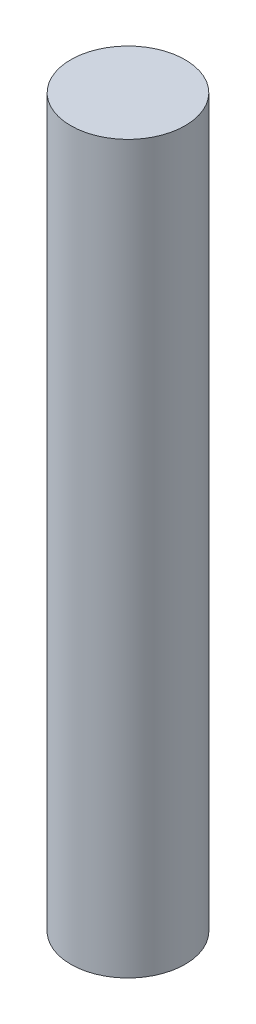
SolidWorks part; units mm, degrees
ref_plane "Front Plane" through (0, 0, 0) normal (0, 0, 1) x (1, 0, 0)
ref_plane "Top Plane" through (0, 0, 0) normal (0, 1, 0) x (1, 0, 0)
ref_plane "Right Plane" through (0, 0, 0) normal (1, 0, 0) x (0, 0, -1)
sketch "Sketch1" plane through (0, 0, 0) normal (0, 1, 0) x (1, 0, 0)
  circle A0 centre (0, 0) radius 4
extrude "Boss-Extrude1" add sketch "Sketch1" along normal blind 50.8 contours A0
